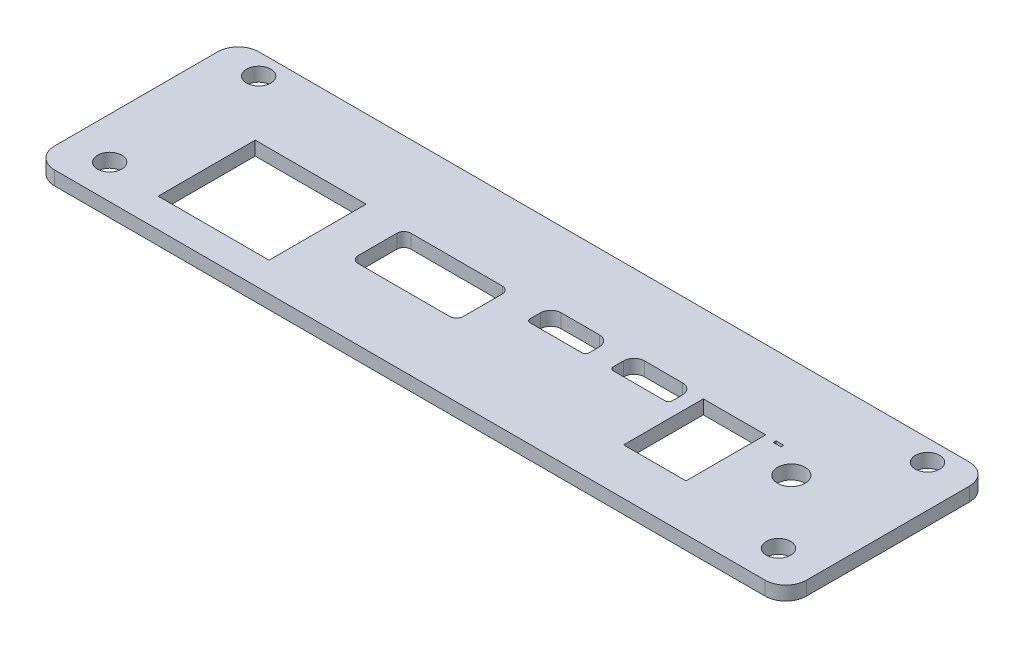
SolidWorks part; units mm, degrees
ref_plane "Front Plane" through (0, 0, 0) normal (0, 0, 1) x (1, 0, 0)
ref_plane "Top Plane" through (0, 0, 0) normal (0, 1, 0) x (1, 0, 0)
ref_plane "Right Plane" through (0, 0, 0) normal (1, 0, 0) x (0, 0, -1)
sketch "Sketch1" plane through (0, 0, 0) normal (0, 1, 0) x (1, 0, 0)
  line L1 (0, 0) -> (108.5, 0)
  line L2 (0, 0) -> (0, 29.5)
  line L3 (0, 29.5) -> (108.5, 29.5)
  line L4 (108.5, 0) -> (108.5, 29.5)
  dimension "D1" = 29.5
  dimension "D2" = 108.5
extrude "Boss-Extrude1" add sketch "Sketch1" along normal blind 2
sketch "Sketch2" plane through (0, 2, 0) normal (0, 1, 0) x (1, 0, 0)
  line L0 (54.25, 29.5) -> (54.25, 0) construction
  line L1 (108.5, 29.5) -> (0, 29.5) construction
  line L2 (0, 0) -> (108.5, 0) construction
  line L3 (0, 14.75) -> (108.5, 14.75) construction
  line L4 (0, 29.5) -> (0, 0) construction
  line L5 (108.5, 0) -> (108.5, 29.5) construction
  circle A0 centre (6, 26.45) radius 1.75
  circle A1 centre (6, 4.95) radius 1.75
  circle A2 centre (102.5, 4.95) radius 1.75
  circle A3 centre (102.5, 26.45) radius 1.75
  dimension "D1" = 3.5
  dimension "D4" = 3.5
  dimension "D2" = 48.25
  dimension "D3" = 11.7
  dimension "D5" = 9.8
  dimension "D6" = 48.25
extrude "Cut-Extrude1" cut sketch "Sketch2" against normal through all
fillet "Fillet1" radius 3 4 edges at (108.5, 1, 0) (108.5, 1, -29.5) (0, 1, 0) (0, 1, -29.5)
sketch "Sketch4" plane through (0, 2, 0) normal (0, 1, 0) x (1, 0, 0)
  line L2 (3, 0) -> (105.5, 0) construction
  line L4 (4, 7.7) -> (104.5, 7.7)
  line L5 (54.25, 29.5) -> (54.25, 0) construction
  line L6 (105.5, 29.5) -> (3, 29.5) construction
  line L7 (4, 7.7) -> (4, 9.7)
  line L8 (4, 9.7) -> (104.5, 9.7)
  line L9 (104.5, 9.7) -> (104.5, 7.7)
  dimension "D3" = 50.25
  dimension "D1" = 50.25
  dimension "D4" = 50.25
  dimension "D5" = 7.7
  dimension "D6" = 2
sketch "Sketch5" plane through (0, 2, 0) normal (0, 1, 0) x (1, 0, 0)
  line L0 (4, 9.7) -> (4, 18.2) construction
  line L1 (4, 18.2) -> (104.5, 18.2) construction
  line L2 (104.5, 18.2) -> (104.5, 9.7) construction
  line L3 (4, 20.2) -> (104.5, 20.2) construction
  line L4 (4, 18.2) -> (4, 20.2) construction
  line L5 (104.5, 18.2) -> (104.5, 20.2) construction
  line L6 (0, 26.5) -> (0, 3) construction
  line L7 (13.75, 18.2) -> (29.75, 18.2)
  line L8 (13.75, 18.2) -> (13.75, 4.2)
  line L9 (13.75, 4.2) -> (29.75, 4.2)
  line L10 (29.75, 18.2) -> (29.75, 4.2)
  line L11 (35.6, 17.8) -> (35.6, 10.2)
  line L12 (50.8, 17.8) -> (50.8, 10.2)
  line L13 (35.6, 10.2) -> (50.8, 10.2)
  line L15 (35.6, 17.8) -> (50.8, 17.8)
  line L16 (55.9033, 18.2) -> (55.9033, 15.2)
  line L17 (55.9033, 15.2) -> (64.4033, 15.2)
  line L18 (64.4033, 18.2) -> (64.4033, 15.2)
  line L19 (88.9033, 18.2) -> (90.0033, 18.2)
  line L20 (67.9033, 18.2) -> (67.9033, 15.2)
  line L21 (67.9033, 15.2) -> (76.4033, 15.2)
  line L22 (76.4033, 18.2) -> (76.4033, 15.2)
  line L23 (78.4033, 18.2) -> (87.4033, 18.2)
  line L24 (78.4033, 18.2) -> (78.4033, 6.7)
  line L25 (78.4033, 6.7) -> (87.4033, 6.7)
  line L26 (87.4033, 18.2) -> (87.4033, 6.7)
  line L27 (108.5, 3) -> (108.5, 26.5) construction
  line L28 (88.9033, 18.2) -> (88.9033, 17.8)
  line L29 (88.9033, 17.8) -> (90.0033, 17.8)
  line L30 (55.9033, 18.2) -> (55.9033, 18.7)
  line L31 (55.9033, 18.7) -> (64.4033, 18.7)
  line L32 (64.4033, 18.2) -> (64.4033, 18.7)
  line L33 (90.0033, 18.2) -> (90.0033, 17.8)
  line L34 (67.9033, 18.2) -> (67.9033, 18.7)
  line L35 (67.9033, 18.7) -> (76.4033, 18.7)
  line L36 (76.4033, 18.2) -> (76.4033, 18.7)
  circle A0 centre (94.3033, 15) radius 2
  point P24 (64.4033, 16.7)
  point P25 (67.9033, 16.7)
  point P30 (76.4033, 16.7)
  point P38 (55.9033, 16.7)
  dimension "D17" = 4
  dimension "D1" = 8.5
  dimension "D3" = 16
  dimension "D4" = 14
  dimension "D5" = 15.2
  dimension "D6" = 5.85
  dimension "D7" = 8
  dimension "D8" = 8.5
  dimension "D9" = 3
  dimension "D10" = 11.5
  dimension "D11" = 8.5
  dimension "D12" = 3
  dimension "D13" = 3.5
  dimension "D14" = 9
  dimension "D15" = 1.1
  dimension "D16" = 2
  dimension "D18" = 6.9
  dimension "D19" = 3.2
  dimension "D20" = 13.75
  dimension "D21" = 14.1967
  dimension "D22" = 108.5
  dimension "D23" = 0.4
  dimension "D24" = 1.5
  dimension "D25" = 64.4033
  dimension "D26" = 55.9033
  dimension "D27" = 0.5
  dimension "D28" = 0.5
  dimension "D29" = 7.6
  dimension "D30" = 4.3
  dimension "D2" = 2
extrude "Cut-Extrude2" cut sketch "Sketch5" against normal through all
fillet "Fillet2" radius 1 4 edges at (35.6, 1, -17.8) (50.8, 1, -17.8) (50.8, 1, -10.2) (35.6, 1, -10.2)
fillet "Fillet3" radius 1.5 4 edges at (76.4033, 1, -18.7) (64.4033, 1, -18.7) (67.9033, 1, -18.7) (55.9033, 1, -18.7)
fillet "Fillet4" radius 0.5 4 edges at (76.4033, 1, -15.2) (64.4033, 1, -15.2) (67.9033, 1, -15.2) (55.9033, 1, -15.2)
